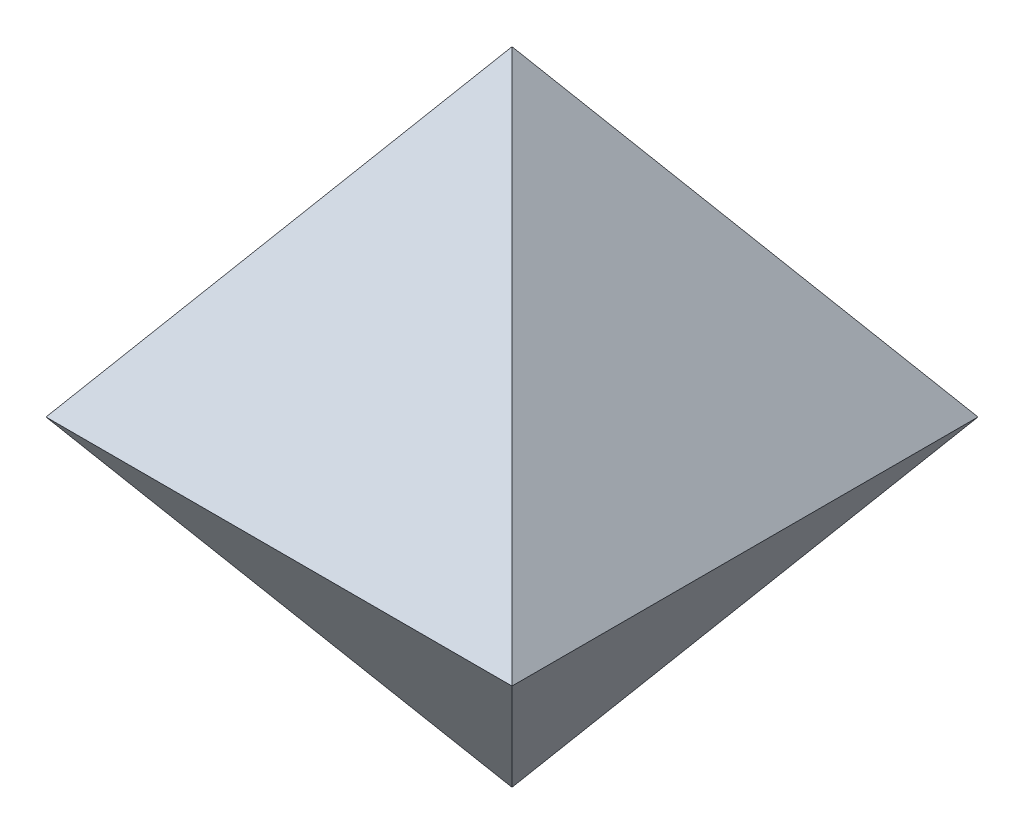
SolidWorks part; units mm, degrees
ref_plane "Front Plane" through (0, 0, 0) normal (0, 0, 1) x (1, 0, 0)
ref_plane "Top Plane" through (0, 0, 0) normal (0, 1, 0) x (1, 0, 0)
ref_plane "Right Plane" through (0, 0, 0) normal (1, 0, 0) x (0, 0, -1)
sketch "Sketch2" plane through (0, 0, 0) normal (0, 1, 0) x (1, 0, 0)
  line L1 (0.5, -0.5) -> (-0.5, -0.5)
  line L2 (0.5, -0.5) -> (0.5, 0.5)
  line L3 (0.5, 0.5) -> (-0.5, 0.5)
  line L4 (-0.5, -0.5) -> (-0.5, 0.5)
  line L5 (0.5, -0.5) -> (-0.5, 0.5) construction
  line L6 (0.5, 0.5) -> (-0.5, -0.5) construction
  point P0 (0, 0)
  dimension "D1" = 1
extrude "Boss-Extrude2" add sketch "Sketch2" along normal blind 1 draft 36
mirror "Mirror2" about plane through (0, 0, 0) normal (0, 1, 0) of "Boss-Extrude2"
